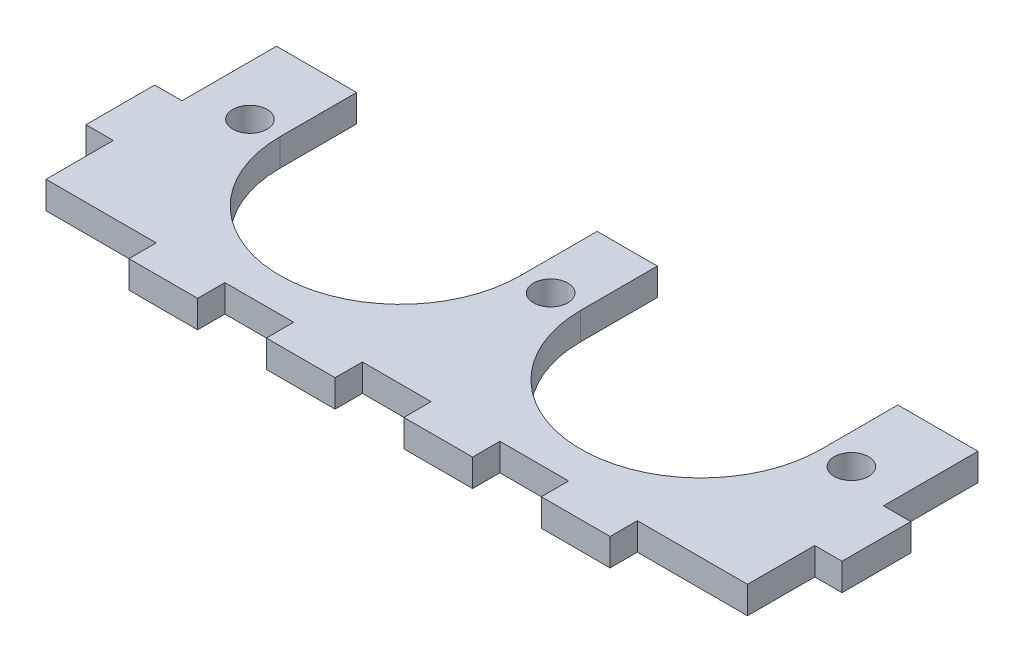
SolidWorks part; units mm, degrees
ref_plane "Front Plane" through (0, 0, 0) normal (0, 0, 1) x (1, 0, 0)
ref_plane "Top Plane" through (0, 0, 0) normal (0, 1, 0) x (1, 0, 0)
ref_plane "Right Plane" through (0, 0, 0) normal (1, 0, 0) x (0, 0, -1)
sketch "Sketch3" plane through (0, 0, 0) normal (0, 1, 0) x (1, 0, 0)
  line L1 (0, 0) -> (88, 0)
  line L2 (0, 0) -> (0, -30)
  line L3 (0, -30) -> (88, -30)
  line L4 (88, 0) -> (88, -30)
  dimension "D1" = 30
  dimension "D2" = 88
extrude "Boss-Extrude1" add sketch "Sketch3" along normal blind 3.175
sketch "Sketch4" plane through (0, 3.175, 0) normal (0, 1, 0) x (1, 0, 0)
  line L0 (44, 0) -> (44, -30) construction
  line L1 (88, 0) -> (0, 0) construction
  line L2 (0, -30) -> (88, -30) construction
  line L3 (0, -15) -> (88, -15) construction
  line L4 (0, 0) -> (0, -30) construction
  line L5 (88, -30) -> (88, 0) construction
  line L6 (16, -30) -> (16, -26.825)
  line L7 (40, -30) -> (48, -30)
  line L8 (0, -26.825) -> (16, -26.825)
  line L9 (40, -26.825) -> (48, -26.825)
  line L10 (48, -30) -> (48, -26.825)
  line L11 (56, -30) -> (64, -30)
  line L12 (56, -30) -> (56, -26.825)
  line L13 (56, -26.825) -> (64, -26.825)
  line L14 (64, -30) -> (64, -26.825)
  line L15 (88, -30) -> (72, -30)
  line L16 (88, -30) -> (88, -26.825)
  line L17 (88, -26.825) -> (72, -26.825)
  line L18 (72, -30) -> (72, -26.825)
  line L19 (0, -30) -> (0, -26.825)
  line L20 (0, -30) -> (16, -30)
  line L21 (24, -30) -> (24, -26.825)
  line L22 (32, -26.825) -> (24, -26.825)
  line L23 (32, -30) -> (32, -26.825)
  line L24 (32, -30) -> (24, -30)
  line L25 (40, -30) -> (40, -26.825)
  line L26 (88, -19) -> (88, -26.825)
  line L27 (0, 0) -> (3.175, 0)
  line L28 (0, 0) -> (0, -11)
  line L29 (0, -11) -> (3.175, -11)
  line L30 (3.175, 0) -> (3.175, -11)
  line L31 (84.825, -19) -> (84.825, -26.825)
  line L32 (88, -19) -> (84.825, -19)
  line L33 (84.825, 0) -> (84.825, -11)
  line L34 (88, -11) -> (84.825, -11)
  line L35 (0, -19) -> (3.175, -19)
  line L36 (0, -19) -> (0, -26.825)
  line L37 (0, -26.825) -> (3.175, -26.825)
  line L38 (3.175, -19) -> (3.175, -26.825)
  line L39 (88, 0) -> (88, -11)
  line L40 (88, 0) -> (84.825, 0)
  line L41 (84.825, -26.825) -> (88, -26.825)
  line L42 (88, -19) -> (88, -26.825)
  point P34 (44, -26.825)
  line M11 (0, 0) -> (0, -30)
  line M12 (0, -30) -> (88, -30)
  line M13 (88, -30) -> (88, 0)
  line M14 (88, 0) -> (0, 0)
  dimension "D1" = 4
  dimension "D2" = 3.175
  dimension "D3" = 8
  dimension "D4" = 3.175
  dimension "D5" = 8
  dimension "D6" = 3.175
  dimension "D7" = 8
  dimension "D8" = 8
extrude "Cut-Extrude1" cut sketch "Sketch4" against normal up to next contours L38 L35 L8 M11 | L8 L6 M11 M12 | L23 L22 L21 M12 | L25 L10 L9 M12 | L14 L13 L12 M12 | L32 L31 L17 M13 | L34 L33 M13 M14 | L18 L17 M12 M13 | L30 L29 M14 M11
sketch "Sketch5" plane through (0, 3.175, 0) normal (0, 1, 0) x (1, 0, 0)
  line L0 (3.175, -22.9125) -> (84.825, -22.9125) construction
  line L1 (3.175, -19) -> (3.175, -26.825) construction
  line L2 (84.825, -19) -> (84.825, -26.825) construction
  line L3 (44, -26.825) -> (44, 0) construction
  line L4 (40, -26.825) -> (48, -26.825) construction
  line L5 (84.825, 0) -> (3.175, 0) construction
  line L6 (3.175, -8.9125) -> (84.825, -8.9125) construction
  line L8 (3.175, 0) -> (3.175, -11) construction
  line L9 (84.825, 0) -> (84.825, -11) construction
  line L10 (75.5, -8.9125) -> (75.5, 0)
  line L11 (47.5, -8.9125) -> (47.5, 0)
  line L12 (47.5, 0) -> (75.5, 0)
  line L13 (75.5, 0) -> (74.5976, -0.0734)
  line L14 (12.5, -8.9125) -> (12.5, 0)
  line L15 (40.5, 0) -> (12.5, 0)
  line L16 (40.5, -8.9125) -> (40.5, 0)
  circle A0 centre (44, -8.9125) radius 2
  circle A1 centre (9, -8.9125) radius 2
  circle A2 centre (79, -8.9125) radius 2
  arc A3 (47.5, -8.9125) -> (75.5, -8.9125) centre (61.5, -8.9125) ccw
  arc A4 (40.5, -8.9125) -> (12.5, -8.9125) centre (26.5, -8.9125) cw
  point P24 (61.5, -8.9125)
  point P25 (47.5, -8.9125)
  line M6 (84.825, 0) -> (3.175, 0)
  dimension "D2" = 4
  dimension "D3" = 4
  dimension "D1" = 14
  dimension "D4" = 35
  dimension "D5" = 17.5
  dimension "D6" = 14
extrude "Cut-Extrude2" cut sketch "Sketch5" against normal up to next contours A4 L16 L14 M6 | A1 | A0 | L11 A3 L10 M6 | A2
